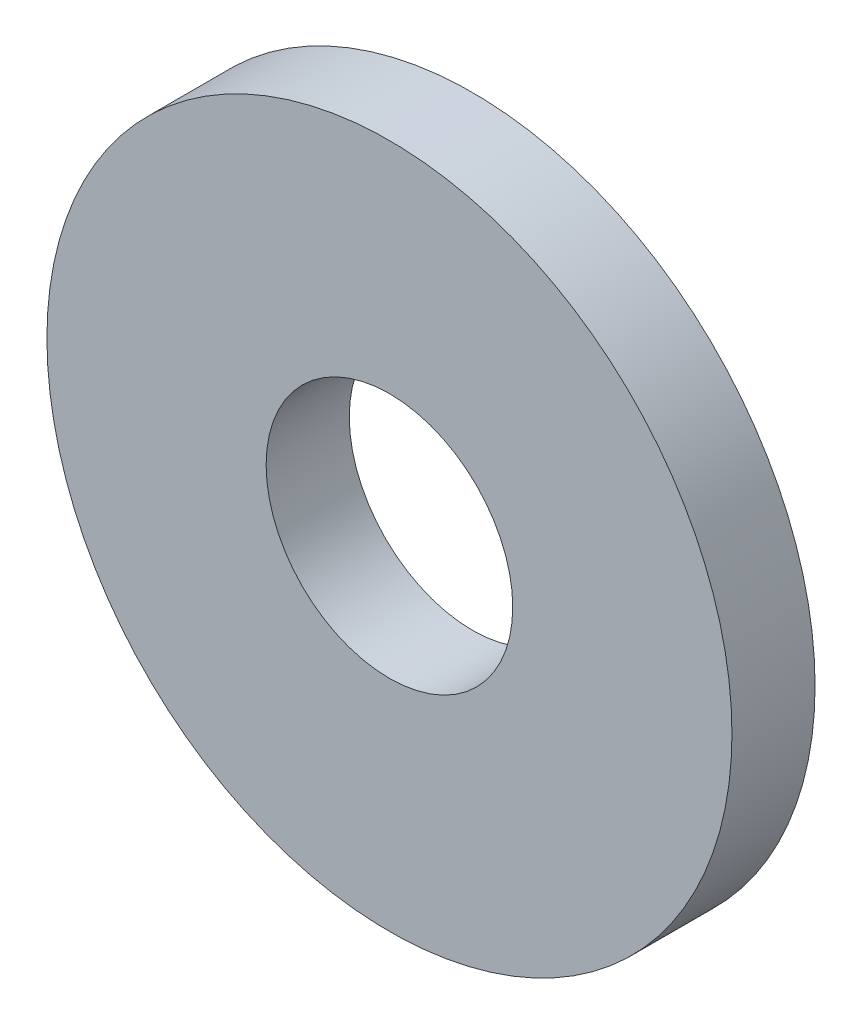
SolidWorks part; units mm, degrees
ref_plane "Front Plane" through (0, 0, 0) normal (0, 0, 1) x (1, 0, 0)
ref_plane "Top Plane" through (0, 0, 0) normal (0, 1, 0) x (1, 0, 0)
ref_plane "Right Plane" through (0, 0, 0) normal (1, 0, 0) x (0, 0, -1)
sketch "Sketch1" plane through (0, 0, 0) normal (0, 0, 1) x (1, 0, 0)
  circle A0 centre (0, 0) radius 9.525
  circle A1 centre (0, 0) radius 3.429
  dimension "D1" = 19.05
  dimension "D2" = 6.858
extrude "Boss-Extrude1" add sketch "Sketch1" along normal blind 2.3114
